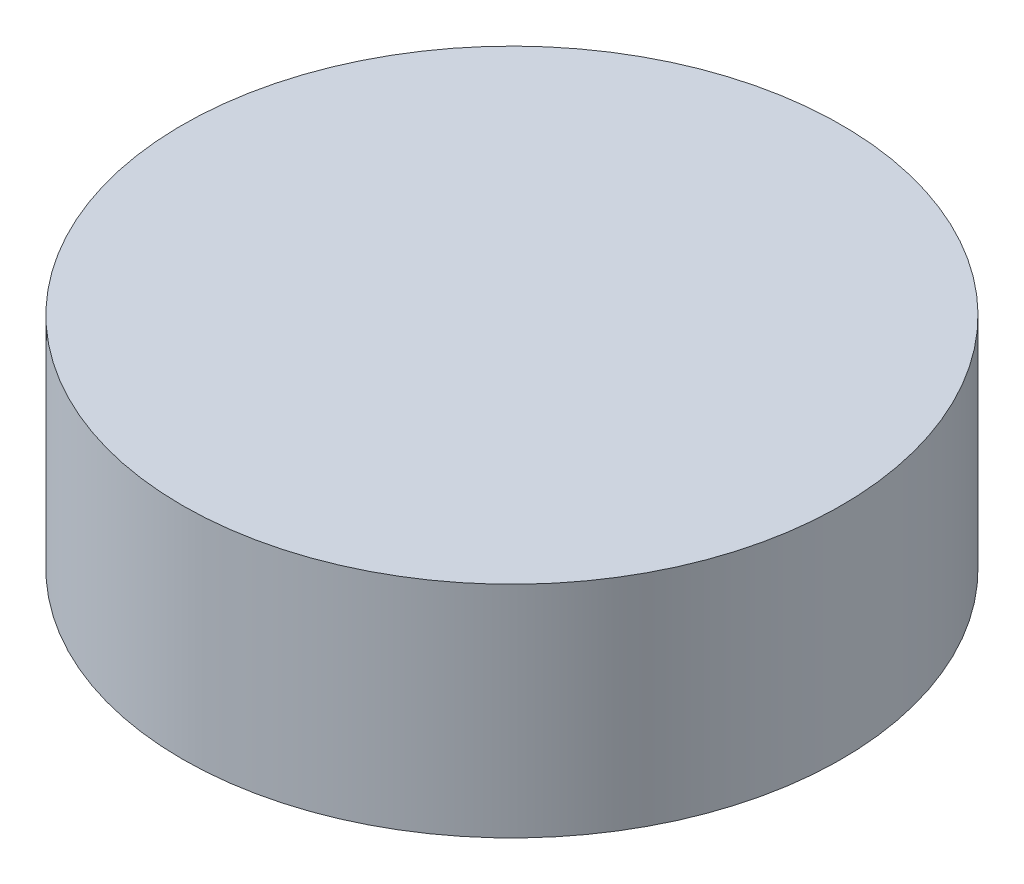
SolidWorks part; units mm, degrees
ref_plane "Front Plane" through (0, 0, 0) normal (0, 0, 1) x (1, 0, 0)
ref_plane "Top Plane" through (0, 0, 0) normal (0, 1, 0) x (1, 0, 0)
ref_plane "Right Plane" through (0, 0, 0) normal (1, 0, 0) x (0, 0, -1)
sketch "Sketch1" plane through (0, 0, 0) normal (0, 1, 0) x (1, 0, 0)
  circle A0 centre (0, 0) radius 1.5
extrude "Boss-Extrude1" add sketch "Sketch1" along normal blind 1
